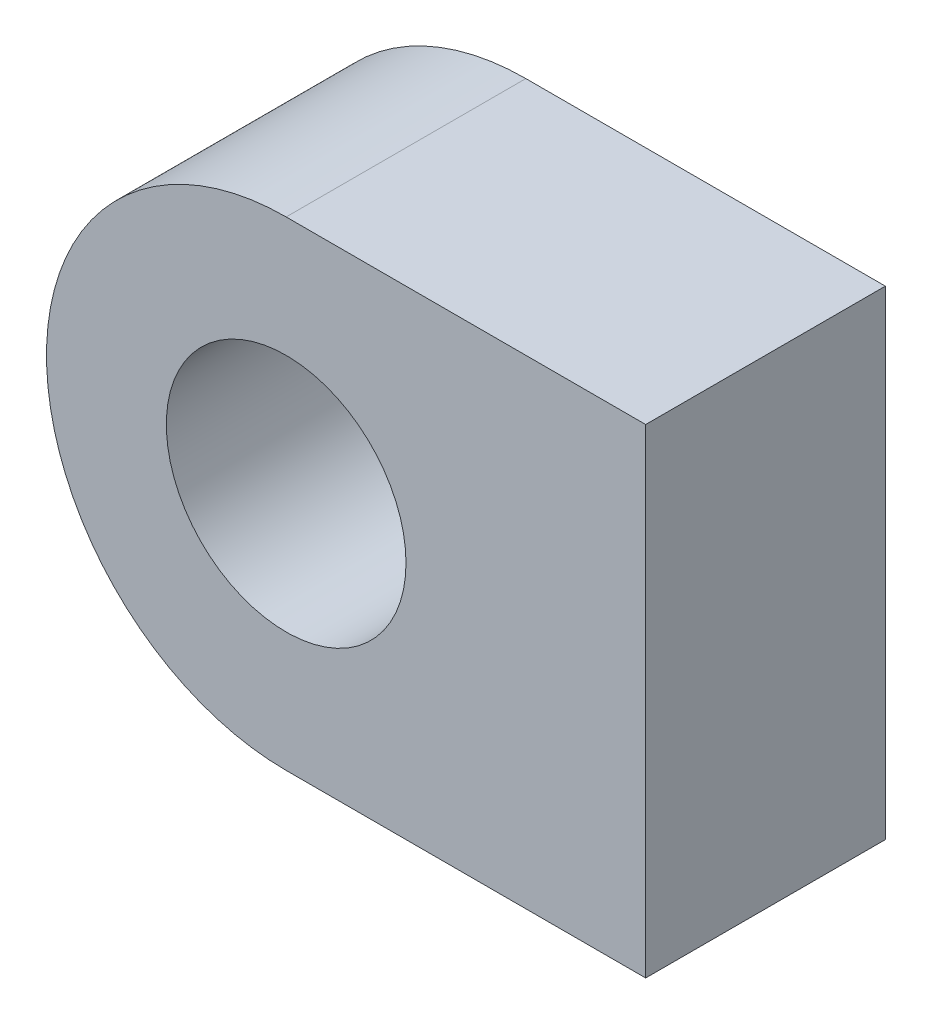
SolidWorks part; units mm, degrees
ref_plane "Front Plane" through (0, 0, 0) normal (0, 0, 1) x (1, 0, 0)
ref_plane "Top Plane" through (0, 0, 0) normal (0, 1, 0) x (1, 0, 0)
ref_plane "Right Plane" through (0, 0, 0) normal (1, 0, 0) x (0, 0, -1)
sketch "Sketch2" plane through (0, 0, 0) normal (0, 0, 1) x (1, 0, 0)
  line L0 (0, 10) -> (0, -10)
  line L1 (0, 10) -> (-15, 10)
  line L2 (-15, -10) -> (0, -10)
  arc A0 (-15, 10) -> (-15, -10) centre (-15, 0) ccw
  circle A1 centre (-15, 0) radius 5
  point P6 (-25, 0)
  dimension "D2" = 10
  dimension "D3" = 10
  dimension "D1" = 25
extrude "Boss-Extrude1" add sketch "Sketch2" against normal blind 10
